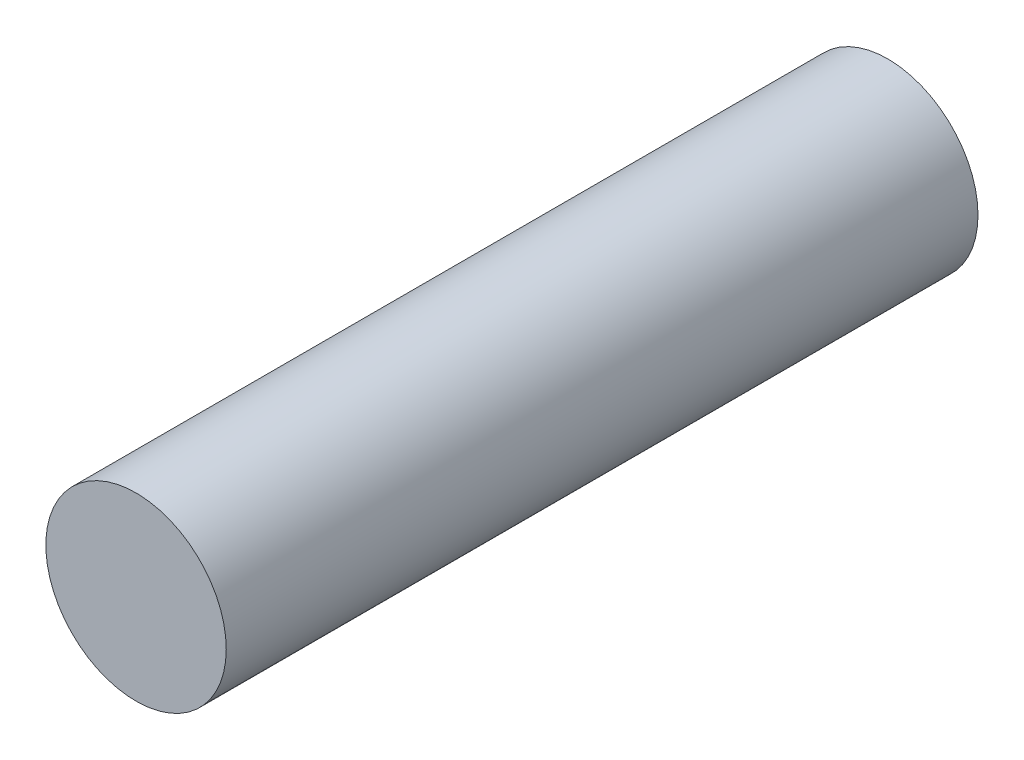
SolidWorks part; units mm, degrees
ref_plane "Front Plane" through (0, 0, 0) normal (0, 0, 1) x (1, 0, 0)
ref_plane "Top Plane" through (0, 0, 0) normal (0, 1, 0) x (1, 0, 0)
ref_plane "Right Plane" through (0, 0, 0) normal (1, 0, 0) x (0, 0, -1)
sketch "Sketch2" plane through (0, 0, 0) normal (0, 0, 1) x (1, 0, 0)
  circle A0 centre (0, 0) radius 6
extrude "Boss-Extrude1" add sketch "Sketch2" along normal blind 50
